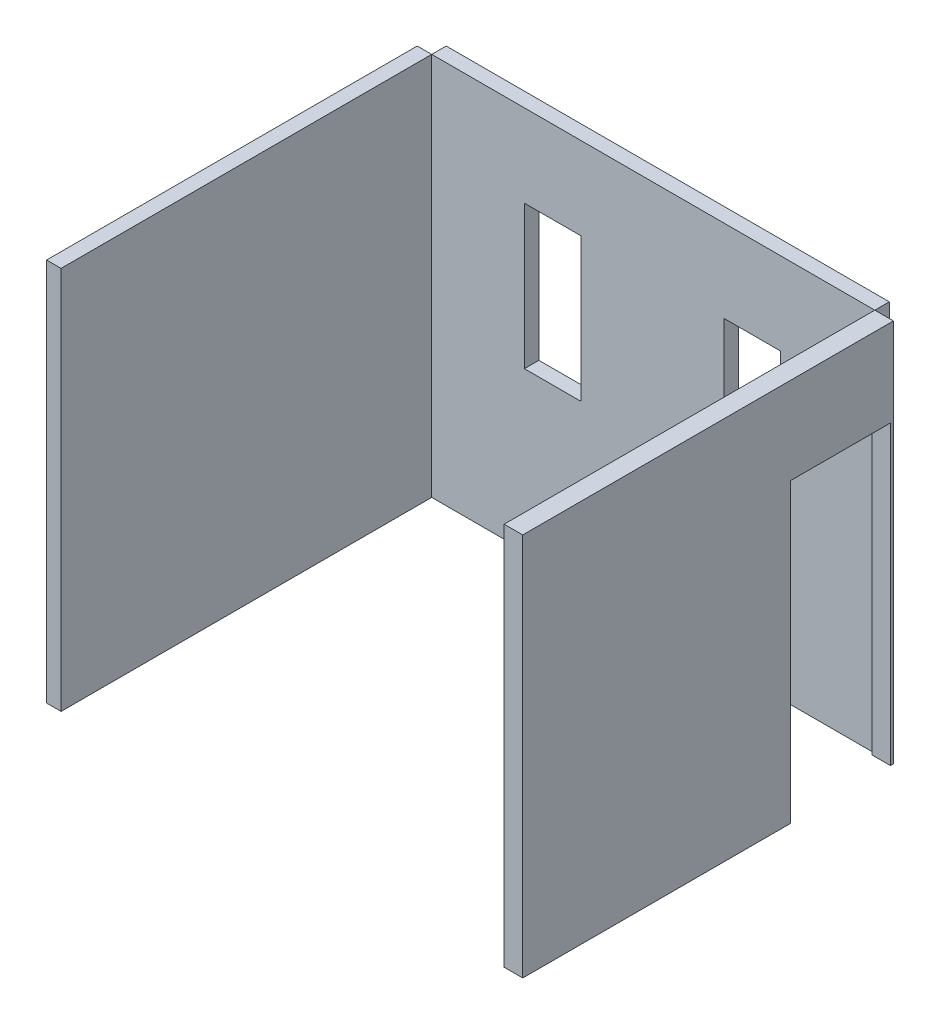
SolidWorks part; units mm, degrees
ref_plane "Plano frontal" through (0, 0, 0) normal (0, 0, 1) x (1, 0, 0)
ref_plane "Plano superior" through (0, 0, 0) normal (0, 1, 0) x (1, 0, 0)
ref_plane "Plano direito" through (0, 0, 0) normal (1, 0, 0) x (0, 0, -1)
sketch "Esboço6" plane through (0, 0, 0) normal (0, 0, 1) x (1, 0, 0)
  line L1 (0, 0) -> (3060, 0)
  line L2 (0, 0) -> (0, 2650)
  line L3 (0, 2650) -> (3060, 2650)
  line L4 (3060, 0) -> (3060, 2650)
extrude "Ressalto-extrusão2" add sketch "Esboço6" along normal blind 100
sketch "Esboço7" plane through (0, 0, 100) normal (0, 0, 1) x (1, 0, 0)
  line L2 (2020, 2080) -> (2020, 1090)
  line L3 (640, 2080) -> (640, 1090)
  line L4 (640, 2080) -> (1030, 2080)
  line L5 (1030, 2080) -> (1030, 1090)
  line L6 (1030, 1090) -> (640, 1090)
  line L7 (2020, 1090) -> (2410, 1090)
  line L8 (2410, 1090) -> (2410, 2080)
  line L9 (2410, 2080) -> (2020, 2080)
extrude "Corte-extrusão1" cut sketch "Esboço7" against normal blind 749
sketch "Esboço8" plane through (0, 0, 100) normal (0, 0, 1) x (1, 0, 0)
  line L1 (0, 2650) -> (-100, 2650)
  line L2 (0, 2650) -> (0, 0)
  line L3 (0, 0) -> (-100, 0)
  line L4 (-100, 2650) -> (-100, 0)
extrude "Ressalto-extrusão3" add sketch "Esboço8" along normal blind 2560 separate body
sketch "Esboço9" plane through (0, 0, 100) normal (0, 0, 1) x (1, 0, 0)
  line L0 (3060, 2650) -> (3188.5515, 2650)
  line L1 (3188.5515, 2650) -> (3188.5515, 0)
  line L2 (3188.5515, 0) -> (3060, 0)
  line L3 (3060, 2650) -> (3060, 0)
extrude "Ressalto-extrusão4" add sketch "Esboço9" along normal blind 2560 separate body
sketch "Esboço12" plane through (3188.5515, 0, 0) normal (1, 0, 0) x (0, 0, -1)
  line L0 (-810, 2050) -> (-120, 2050)
  line L3 (-810, 0) -> (-120, 0)
  line L4 (-810, 2050) -> (-810, 0)
  line L5 (-2660, 0) -> (-100, 0) construction
  line L6 (-120, 0) -> (-120, 2050)
extrude "Corte-extrusão2" cut sketch "Esboço12" against normal blind 1050
ref_plane "Plano1" through (3060, 2650, 100) normal (0, 1, 0) x (1, 0, 0)
